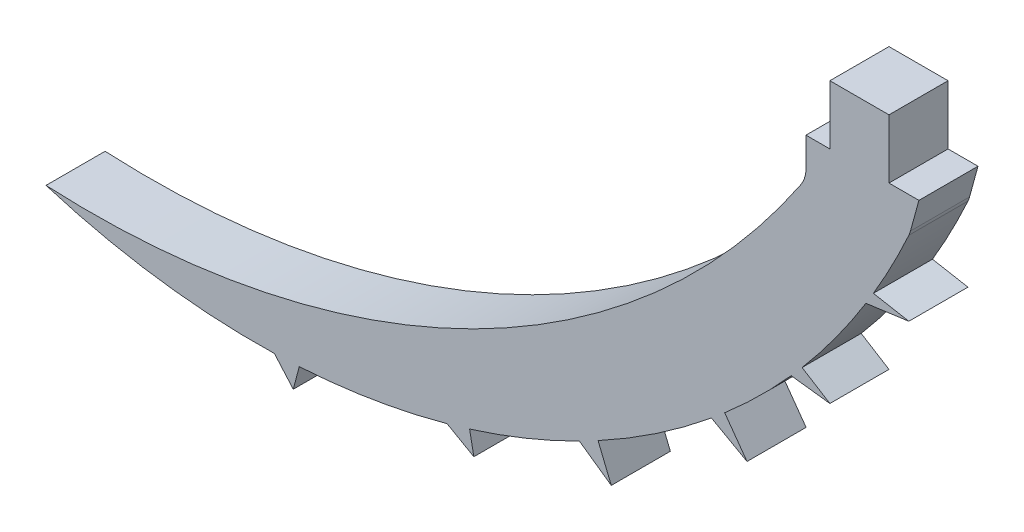
SolidWorks part; units mm, degrees
ref_plane "Front Plane" through (0, 0, 0) normal (0, 0, 1) x (1, 0, 0)
ref_plane "Top Plane" through (0, 0, 0) normal (0, 1, 0) x (1, 0, 0)
ref_plane "Right Plane" through (0, 0, 0) normal (1, 0, 0) x (0, 0, -1)
sketch "Sketch1" plane through (0, 0, 0) normal (0, 0, 1) x (1, 0, 0)
  line L0 (-4.3377, 0) -> (-4.3377, 1.524)
  line L1 (-4.3377, 1.524) -> (-5.8617, 1.524)
  line L2 (-5.8617, 1.524) -> (-5.8617, 0)
  line L3 (-5.8617, 0) -> (-6.4783, 0)
  line L4 (-4.3377, 0) -> (-3.5658, 0)
  line L5 (-3.5658, 0) -> (-3.7836, -0.7948)
  line L6 (-6.4783, 0) -> (-6.4783, -0.7431)
  line L7 (-20.1875, -11.7318) -> (-19.7007, -12.2872)
  line L8 (-19.7007, -12.2872) -> (-19.5471, -11.7046)
  line L9 (-15.7356, -11.0725) -> (-15.0438, -11.4662)
  line L10 (-15.0438, -11.4662) -> (-15.1544, -10.9019)
  line L11 (-12.322, -9.7555) -> (-11.4996, -10.3341)
  line L12 (-11.4996, -10.3341) -> (-11.8402, -9.5035)
  line L13 (-8.9163, -7.5363) -> (-7.9989, -8.0496)
  line L14 (-7.9989, -8.0496) -> (-8.5741, -7.2482)
  line L15 (-6.8603, -5.5631) -> (-5.8617, -5.6859)
  line L16 (-5.8617, -5.6859) -> (-6.5789, -5.2405)
  line L17 (-4.9332, -2.9833) -> (-3.8249, -2.8305)
  line L18 (-3.8249, -2.8305) -> (-4.7398, -2.6638)
  arc A0 (-6.6071, -1.167) -> (-26.0781, -10.9223) centre (-24.9319, 11.0991) cw
  arc A1 (-26.0781, -10.9223) -> (-20.1875, -11.7318) centre (-20.6493, 6.7468) ccw
  arc A2 (-3.7836, -0.7948) -> (-3.8249, -0.909) centre (-4.5185, -0.5934) cw
  arc A3 (-6.4783, -0.7431) -> (-6.6071, -1.167) centre (-7.2403, -0.7431) cw
  arc A4 (-19.5471, -11.7046) -> (-15.7356, -11.0725) centre (-20.6493, 6.7468) ccw
  arc A5 (-15.1544, -10.9019) -> (-12.322, -9.7555) centre (-20.6493, 6.7468) ccw
  arc A6 (-11.8402, -9.5035) -> (-8.9163, -7.5363) centre (-20.6493, 6.7468) ccw
  arc A7 (-8.5741, -7.2482) -> (-6.8603, -5.5631) centre (-20.6493, 6.7468) ccw
  arc A8 (-4.7398, -2.6638) -> (-3.8249, -0.909) centre (-20.6493, 6.7468) ccw
  arc A9 (-6.5789, -5.2405) -> (-4.9332, -2.9833) centre (-20.6493, 6.7468) ccw
  dimension "D1" = 0.762
extrude "Boss-Extrude1" add sketch "Sketch1" along normal blind 1.524
